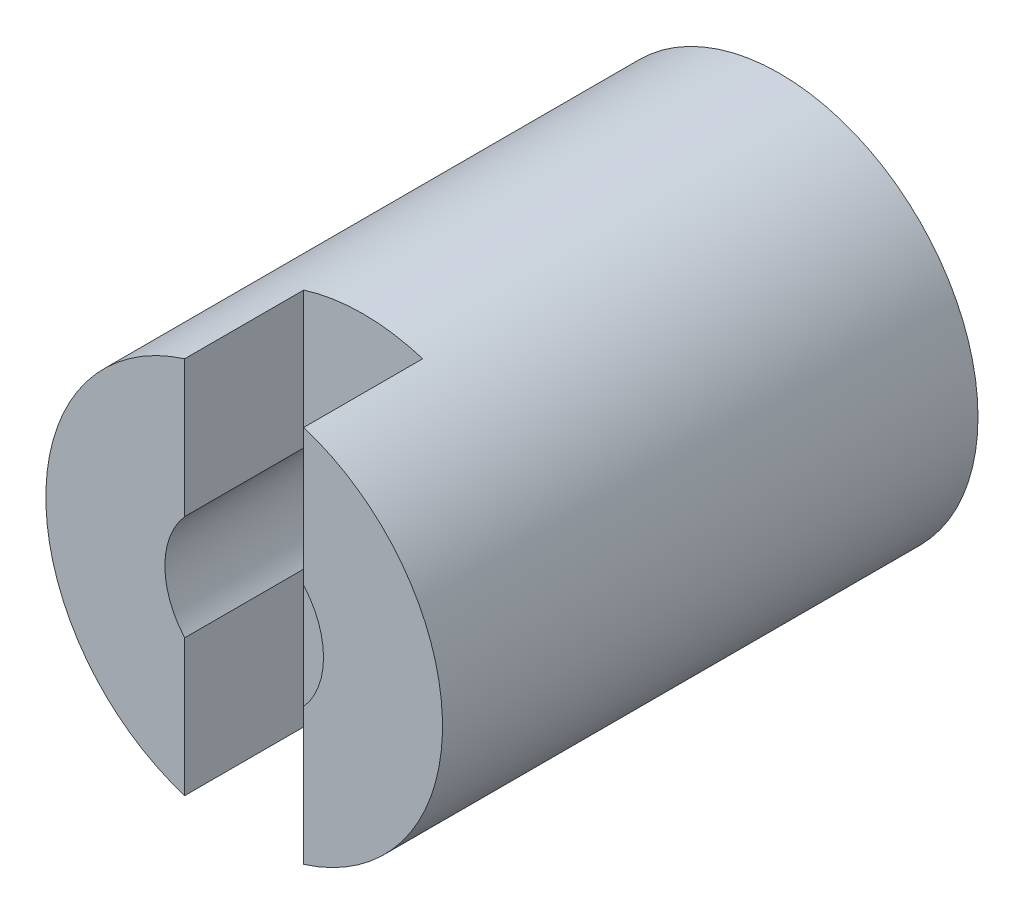
SolidWorks part; units mm, degrees
material "201 Annealed Stainless Steel (SS)"
ref_plane "Front" through (0, 0, 0) normal (0, 0, 1) x (1, 0, 0)
ref_plane "Top" through (0, 0, 0) normal (0, 1, 0) x (1, 0, 0)
ref_plane "Right" through (0, 0, 0) normal (1, 0, 0) x (0, 0, -1)
sketch "Sketch1" plane through (0, 0, 0) normal (0, 0, 1) x (1, 0, 0)
  circle A0 centre (0, 0) radius 10
  dimension "D1" = 20
extrude "Boss-Extrude1" add sketch "Sketch1" along normal blind 27
sketch "Sketch2" plane through (0, 0, 27) normal (0, 0, 1) x (1, 0, 0)
  circle A0 centre (0, 0) radius 4
  dimension "D1" = 8
extrude "Cut-Extrude1" cut sketch "Sketch2" against normal blind 140
sketch "Sketch3" plane through (0, 0, 0) normal (0, 0, -1) x (-1, 0, 0)
  circle A0 centre (0, 0) radius 6
  dimension "D1" = 12
extrude "Cut-Extrude2" cut sketch "Sketch3" against normal blind 15
sketch "Sketch4" plane through (0, 0, 0) normal (0, 1, 0) x (1, 0, 0)
  line L0 (-10, -27) -> (10, -27) construction
  line L1 (3, -27) -> (-3, -27)
  line L2 (3, -27) -> (3, -21)
  line L3 (3, -21) -> (-3, -21)
  line L4 (-3, -27) -> (-3, -21)
  point P6 (0, -27)
  dimension "D1" = 6
  dimension "D2" = 6
extrude "Cut-Extrude3" cut sketch "Sketch4" against normal mid plane 30
sketch "Sketch5" plane through (0, 0, 0) normal (0, 0, -1) x (-1, 0, 0)
  line L1 (3.9203, 2.5) -> (7.5, 2.5)
  line L2 (3.9203, 2.5) -> (3.9203, -2.5)
  line L3 (3.9203, -2.5) -> (7.5, -2.5)
  line L4 (7.5, 2.5) -> (7.5, -2.5)
  circle A0 centre (0, 0) radius 6 construction
  point P6 (7.5, 0)
  dimension "D1" = 1.5
  dimension "D2" = 5
  dimension "D3" = 3.5797
extrude "Cut-Extrude4" cut sketch "Sketch5" against normal up to surface (15 mm away) up to face at (-6, 0, 15)
